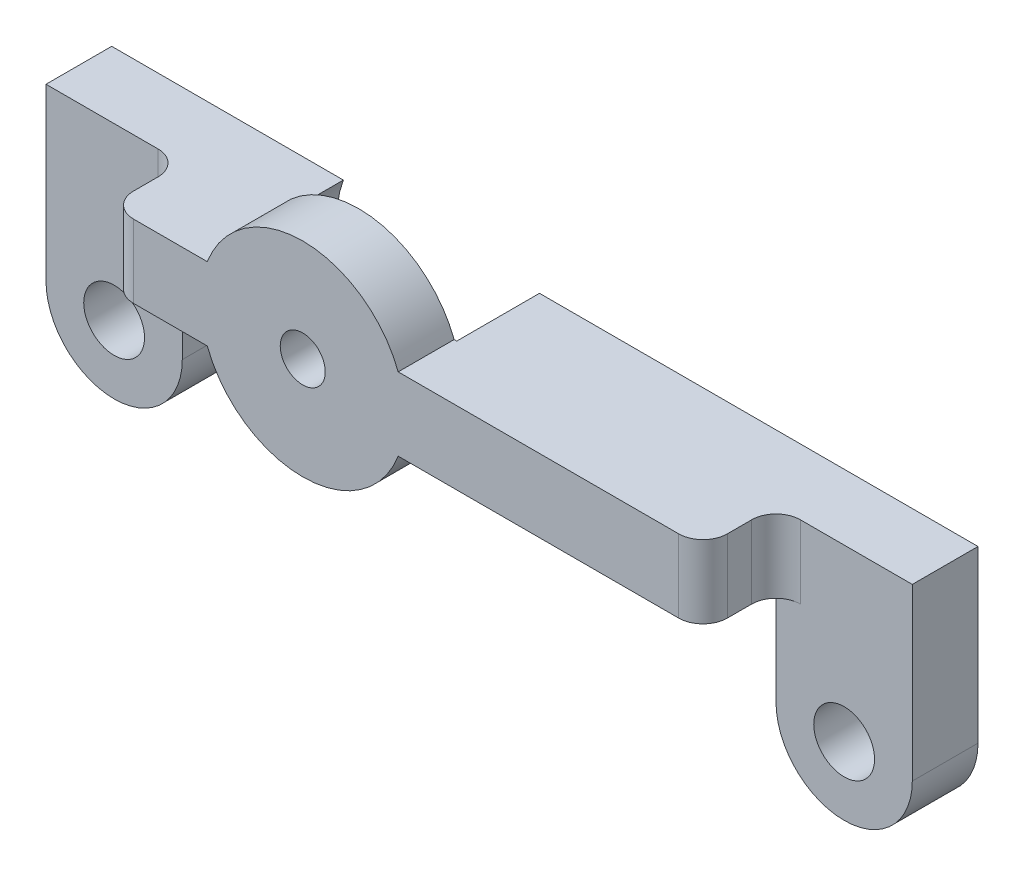
SolidWorks part; units mm, degrees
ref_plane "前视基准面" through (0, 0, 0) normal (0, 0, 1) x (1, 0, 0)
ref_plane "上视基准面" through (0, 0, 0) normal (0, 1, 0) x (1, 0, 0)
ref_plane "右视基准面" through (0, 0, 0) normal (1, 0, 0) x (0, 0, -1)
sketch "草图1" plane through (0, 0, 0) normal (0, 0, 1) x (1, 0, 0)
  line L0 (-12.2, 0.4323) -> (-8.173, 0.4323)
  line L1 (-12.2, -6.5677) -> (-12.2, -3.0677)
  line L2 (-12.2, -6.5677) -> (-12.2, -2.5677)
  line L3 (-12.2, -2.5677) -> (-8.173, -2.5677)
  line L4 (-12.2, -6.5677) -> (-12.2, -2.5677)
  line L5 (-12.2, 0.4323) -> (-17.8, 0.4323)
  line L6 (12.2, -6.5677) -> (12.2, -2.5677)
  line L7 (-17.8, 0.4323) -> (-17.8, -6.5677)
  line L8 (12.2, 0.4323) -> (17.8, 0.4323)
  line L9 (17.8, 0.4323) -> (17.8, -6.5677)
  line L10 (12.2, 0.4323) -> (-0.327, 0.4323)
  line L11 (12.2, -2.5677) -> (-0.327, -2.5677)
  arc A0 (-17.8, -6.5677) -> (-12.2, -6.5677) centre (-15, -6.5677) ccw
  circle A1 centre (-15, -6.5677) radius 1.25
  arc A2 (-8.173, -2.5677) -> (-0.327, -2.5677) centre (-4.25, -1.0677) ccw
  circle A3 centre (-4.25, -1.0677) radius 0.925
  circle A4 centre (15, -6.5677) radius 1.25
  arc A5 (17.8, -6.5677) -> (12.2, -6.5677) centre (15, -6.5677) cw
  arc A6 (-0.327, 0.4323) -> (-8.173, 0.4323) centre (-4.25, -1.0677) ccw
  dimension "D4" = 4
  dimension "D2" = 4
  dimension "D1" = 7
  dimension "D3" = 5.6
extrude "凸台-拉伸1" add sketch "草图1" along normal blind 7.7
sketch "草图2" plane through (0, 0, 0) normal (0, 0, -1) x (-1, 0, 0)
  circle A0 centre (4.25, -1.0677) radius 4.3
extrude "切除-拉伸1" cut sketch "草图2" against normal blind 3.4
sketch "草图3" plane through (0, 0, 7.7) normal (0, 0, 1) x (1, 0, 0)
  line L0 (-17.8, 0.4323) -> (-12.2, 0.4323)
  line L1 (-17.8, 0.4323) -> (-8.173, 0.4323) construction
  line L2 (-12.2, 0.4323) -> (-12.2, -6.5677)
  line L3 (-17.8, -6.5677) -> (-17.8, 0.4323)
  line L4 (12.2, 0.4323) -> (17.8, 0.4323)
  line L5 (-0.327, 0.4323) -> (17.8, 0.4323) construction
  line L6 (17.8, 0.4323) -> (17.8, -6.5677)
  line L7 (12.2, -6.5677) -> (12.2, 0.4323)
  arc A0 (-12.2, -6.5677) -> (-17.8, -6.5677) centre (-15, -6.5677) cw
  arc A1 (-17.8, -6.5677) -> (-12.2, -6.5677) centre (-15, -6.5677) ccw construction
  arc A2 (17.8, -6.5677) -> (12.2, -6.5677) centre (15, -6.5677) cw
  arc A3 (12.2, -6.5677) -> (17.8, -6.5677) centre (15, -6.5677) ccw construction
extrude "切除-拉伸2" cut sketch "草图3" against normal blind 5
sketch "草图5" plane through (0, 0, 7.7) normal (0, 0, 1) x (1, 0, 0)
  line L0 (12.2, -2.5677) -> (-0.327, -2.5677) construction
  line L1 (12.2, 0.4323) -> (-0.327, 0.4323) construction
  line L2 (12.2, 0.4323) -> (12.2, -2.5677) construction
  line L3 (-12.2, 0.4323) -> (-8.173, 0.4323) construction
  line L4 (-12.2, -2.5677) -> (-8.173, -2.5677) construction
  line L5 (-12.2, -2.5677) -> (-12.2, 0.4323) construction
  line L6 (12.2, -2.5677) -> (-0.327, -2.5677)
  line L7 (12.2, 0.4323) -> (-0.327, 0.4323)
  line L8 (12.2, 0.4323) -> (12.2, -2.5677)
  line L9 (-12.2, 0.4323) -> (-8.173, 0.4323)
  line L10 (-12.2, -2.5677) -> (-8.173, -2.5677)
  line L11 (-12.2, -2.5677) -> (-12.2, 0.4323)
  arc A0 (-8.173, -2.5677) -> (-0.327, -2.5677) centre (-4.25, -1.0677) ccw construction
  arc A1 (-0.327, 0.4323) -> (-8.173, 0.4323) centre (-4.25, -1.0677) ccw construction
  arc A2 (-8.173, -2.5677) -> (-0.327, -2.5677) centre (-4.25, -1.0677) ccw
  arc A3 (-0.327, 0.4323) -> (-8.173, 0.4323) centre (-4.25, -1.0677) ccw
extrude "切除-拉伸3" cut sketch "草图5" against normal blind 2
fillet "圆角2" radius 1 4 edges at (12.2, -1.0677, 5.7) (12.2, -1.0677, 2.7) (-12.2, -1.0677, 5.7) (-12.2, -1.0677, 2.7)
